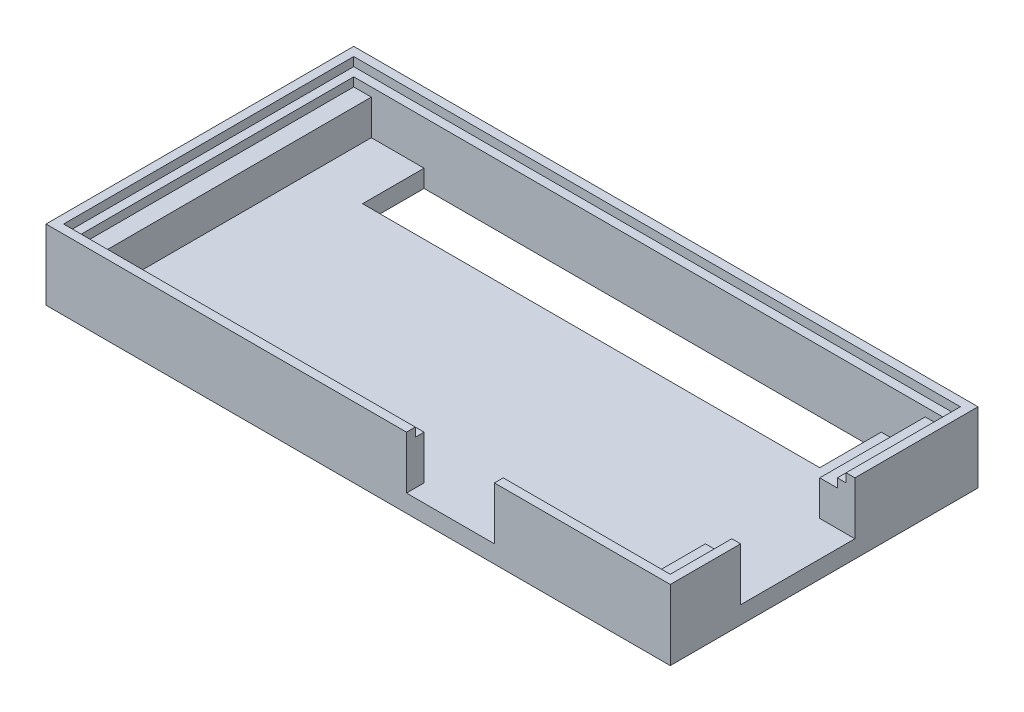
SolidWorks part; units mm, degrees
ref_plane "Front Plane" through (0, 0, 0) normal (0, 0, 1) x (1, 0, 0)
ref_plane "Top Plane" through (0, 0, 0) normal (0, 1, 0) x (1, 0, 0)
ref_plane "Right Plane" through (0, 0, 0) normal (1, 0, 0) x (0, 0, -1)
sketch "Sketch1" plane through (0, 0, 0) normal (0, 1, 0) x (1, 0, 0)
  line L0 (0, 0) -> (71, 0)
  line L1 (71, 0) -> (71, 35)
  line L2 (71, 35) -> (0, 35)
  line L3 (0, 35) -> (0, 0)
  dimension "D1" = 35
  dimension "D2" = 71
extrude "Boss-Extrude1" add sketch "Sketch1" along normal blind 2
sketch "Sketch2" plane through (0, 2, 0) normal (0, 1, 0) x (1, 0, 0)
  line L0 (69, 33) -> (2, 33)
  line L1 (2, 33) -> (2, 2)
  line L2 (2, 2) -> (69, 2)
  line L3 (69, 2) -> (69, 33)
  line L4 (0, 35) -> (0, 0)
  line L5 (0, 0) -> (71, 0)
  line L6 (71, 0) -> (71, 35)
  line L7 (71, 35) -> (0, 35)
  line L8 (0, 35) -> (0, 0)
  line L9 (0, 0) -> (71, 0)
  line L10 (71, 0) -> (71, 35)
  line L11 (71, 35) -> (0, 35)
  dimension "D1" = 0
  dimension "D2" = 2
extrude "Boss-Extrude2" add sketch "Sketch2" along normal blind 5
sketch "Sketch3" plane through (0, 2, 0) normal (0, 1, 0) x (1, 0, 0)
  line L0 (10, 33) -> (10, 26)
  line L1 (69, 33) -> (2, 33) construction
  line L2 (10, 26) -> (62, 26)
  line L3 (62, 26) -> (62, 33)
  line L4 (69, 33) -> (2, 33) construction
  line L5 (62, 33) -> (10, 33)
  line L7 (69, 2) -> (69, 33) construction
  dimension "D1" = 7
  dimension "D2" = 52
  dimension "D3" = 7
extrude "Cut-Extrude1" cut sketch "Sketch3" against normal blind 5
sketch "Sketch4" plane through (0, 2, 0) normal (0, 1, 0) x (1, 0, 0)
  line L0 (2, 33) -> (4, 33)
  line L1 (10, 33) -> (2, 33) construction
  line L2 (4, 33) -> (4, 2)
  line L3 (2, 2) -> (69, 2) construction
  line L4 (4, 2) -> (2, 2)
  line L5 (2, 2) -> (2, 33)
  line L6 (69, 33) -> (67, 33)
  line L7 (69, 33) -> (62, 33) construction
  line L8 (67, 33) -> (67, 21)
  line L9 (67, 21) -> (69, 21)
  line L10 (69, 2) -> (69, 33) construction
  line L11 (69, 21) -> (69, 33)
  line L12 (69, 2) -> (67, 2)
  line L13 (2, 2) -> (69, 2) construction
  line L14 (67, 2) -> (67, 8)
  line L15 (67, 8) -> (69, 8)
  line L16 (69, 2) -> (69, 33) construction
  line L17 (69, 8) -> (69, 2)
  dimension "D1" = 2
  dimension "D2" = 2
  dimension "D3" = 12
  dimension "D4" = 2
  dimension "D5" = 6
extrude "Boss-Extrude3" add sketch "Sketch4" along normal blind 4
sketch "Sketch5" plane through (69, 0, 0) normal (-1, 0, 0) x (0, 0, 1)
  line L0 (-21, 2) -> (-21, 7)
  line L1 (-2, 7) -> (-33, 7) construction
  line L2 (-21, 7) -> (-8, 7)
  line L3 (-8, 7) -> (-8, 2)
  line L4 (-8, 2) -> (-21, 2)
extrude "Cut-Extrude2" cut sketch "Sketch5" against normal blind 2
sketch "Sketch6" plane through (0, 0, -2) normal (0, 0, -1) x (-1, 0, 0)
  line L0 (-51, 7) -> (-51, 2)
  line L2 (-2, 7) -> (-69, 7) construction
  line L3 (-4, 2) -> (-67, 2) construction
  line L4 (-51, 2) -> (-41, 2)
  line L5 (-41, 2) -> (-41, 7)
  line L6 (-41, 7) -> (-51, 7)
  dimension "D1" = 18
  dimension "D2" = 10
extrude "Cut-Extrude3" cut sketch "Sketch6" against normal blind 2
sketch "Sketch7" plane through (0, 7, 0) normal (0, 1, 0) x (1, 0, 0)
  line L0 (71, 35) -> (0, 35) construction
  line L1 (0, 35) -> (0, 0) construction
  line L2 (0, 0) -> (41, 0) construction
  line L3 (51, 0) -> (71, 0) construction
  line L4 (71, 0) -> (71, 8) construction
  line L5 (71, 21) -> (71, 35) construction
  line L6 (71, 35) -> (0, 35)
  line L7 (0, 35) -> (0, 0)
  line L8 (0, 0) -> (41, 0)
  line L9 (51, 0) -> (71, 0)
  line L10 (71, 0) -> (71, 8)
  line L11 (71, 21) -> (71, 35)
  line L12 (70, 21) -> (70, 34)
  line L13 (70, 34) -> (1, 34)
  line L14 (1, 34) -> (1, 1)
  line L15 (1, 1) -> (41, 1)
  line L16 (41, 1) -> (41, 0)
  line L17 (70, 21) -> (71, 21)
  line L18 (51, 1) -> (70, 1)
  line L19 (70, 1) -> (70, 8)
  line L20 (70, 8) -> (71, 8)
  line L21 (51, 1) -> (51, 0)
  dimension "D1" = 1
  dimension "D2" = 1
extrude "Boss-Extrude4" add sketch "Sketch7" along normal blind 1
